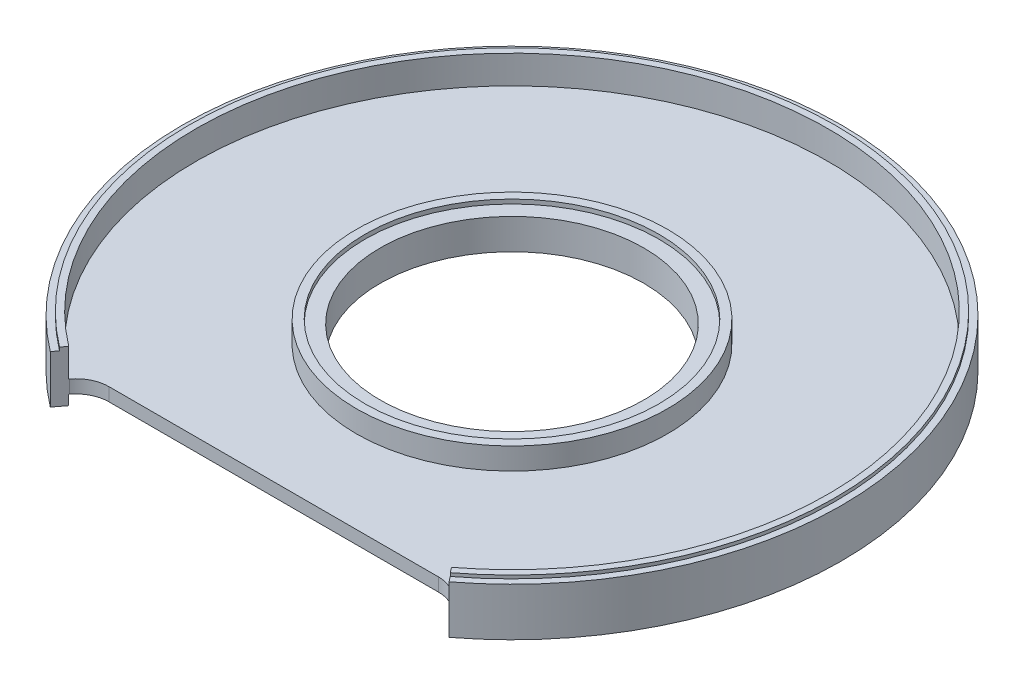
SolidWorks part; units mm, degrees
material "ABS"
ref_plane "Front Plane" through (0, 0, 0) normal (0, 0, 1) x (1, 0, 0)
ref_plane "Top Plane" through (0, 0, 0) normal (0, 1, 0) x (1, 0, 0)
ref_plane "Right Plane" through (0, 0, 0) normal (1, 0, 0) x (0, 0, -1)
sketch "Sketch2" plane through (0, 0, 0) normal (1, 0, 0) x (0, 0, -1)
  line L0 (1.1, 0) -> (-1.1, 0) construction
  line L1 (-50, 3.65) -> (-48, 3.65)
  line L2 (-50, 3.65) -> (-50, -3.65)
  line L3 (-50, -3.65) -> (-48, -3.65)
  line L4 (-48, 3.65) -> (-48, -3.65)
  line L5 (-50, 3.65) -> (-48, -3.65) construction
  line L6 (-50, -3.65) -> (-48, 3.65) construction
  line L7 (0, 0) -> (0, 1.979)
  line L8 (-48, 3.65) -> (-49, 3.65)
  line L9 (-48, 3.65) -> (-48, 4.15)
  line L10 (-48, 4.15) -> (-49, 4.15)
  line L11 (-49, 3.65) -> (-49, 4.15)
  line L12 (-48, -0.15) -> (-20, -0.15)
  line L13 (-48, -0.15) -> (-48, -2.15)
  line L14 (-48, -2.15) -> (-20, -2.15)
  line L15 (-20, -0.15) -> (-20, -2.15)
  line L16 (-23.6, 2.5) -> (-20, 2.5)
  line L17 (-23.6, 2.5) -> (-23.6, -0.15)
  line L18 (-23.6, -0.15) -> (-20, -0.15)
  line L19 (-20, 2.5) -> (-20, -0.15)
  line L20 (-23.6, 2.5) -> (-22.3, 2.5)
  line L21 (-23.6, 2.5) -> (-23.6, 3.15)
  line L22 (-23.6, 3.15) -> (-22.3, 3.15)
  line L23 (-22.3, 2.5) -> (-22.3, 3.15)
  point P0 (-49, 0)
  dimension "D2" = 2
  dimension "D3" = 0
  dimension "D4" = 1
  dimension "D5" = 50
  dimension "D6" = 0
  dimension "D7" = 3.3
  dimension "D8" = 2
  dimension "D9" = 30
  dimension "D10" = 0
  dimension "D11" = 0
  dimension "D12" = 3.6
  dimension "D13" = 2.65
  dimension "D14" = 1.3
  dimension "D15" = 0.5
  dimension "D16" = 1.5
  dimension "D17" = 5.8
revolve "Revolve1" add sketch "Sketch2" angle 360 about L7
sketch "Sketch3" plane through (0, 0, 0) normal (0, 1, 0) x (1, 0, 0)
  line L0 (0, -1.1) -> (0, 1.1) construction
  line L1 (-25, -36.1619) -> (25, -36.1619)
  line L6 (-28.9809, -38.1367) -> (-30.2522, -39.8096)
  line L8 (28.981, -38.1367) -> (30.2522, -39.8096)
  arc A1 (-25, -36.1619) -> (-28.9809, -38.1367) centre (-25, -41.1619) ccw
  arc A4 (25, -36.1619) -> (28.981, -38.1367) centre (25, -41.1619) cw
  point P11 (0, -36.1619)
  dimension "D4" = 10
  dimension "D6" = 5
  dimension "D2" = 36.1619
extrude "Cut-Extrude2" cut sketch "Sketch3" against normal through all and the other way through all flip side to cut
